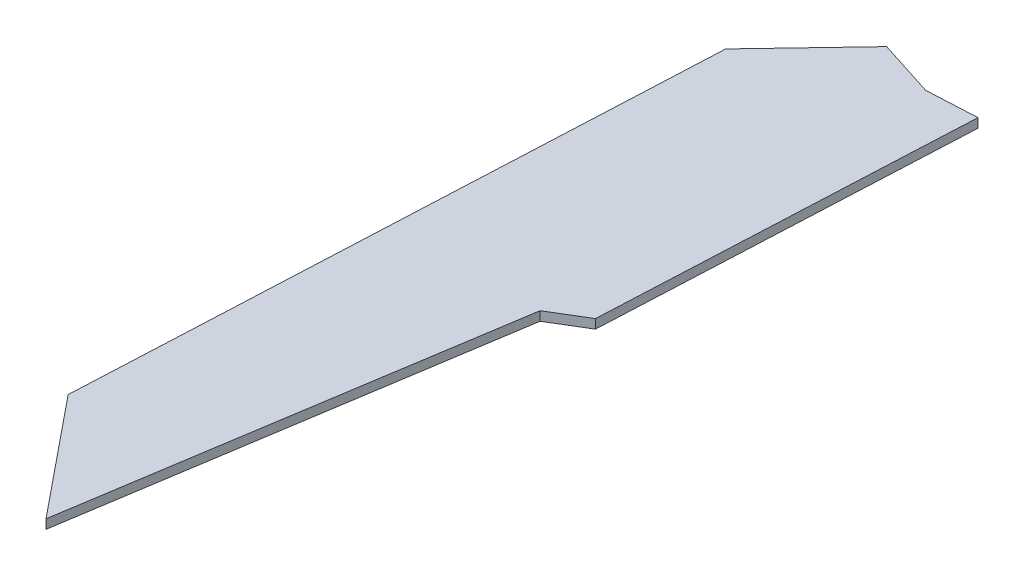
SolidWorks part; units mm, degrees
ref_plane "Plan de face" through (0, 0, 0) normal (0, 0, 1) x (1, 0, 0)
ref_plane "Plan de dessus" through (0, 0, 0) normal (0, 1, 0) x (1, 0, 0)
ref_plane "Plan de droite" through (0, 0, 0) normal (1, 0, 0) x (0, 0, -1)
sketch "Esquisse1" plane through (0, 0, 0) normal (0, 1, 0) x (1, 0, 0)
  line L0 (46.9058, 151.5265) -> (36.038, 150.9785)
  line L1 (36.038, 150.9785) -> (23.5382, 154.9847)
  line L2 (23.5382, 154.9847) -> (6.4202, 136.985)
  line L3 (6.4202, 136.985) -> (0, 0)
  line L4 (0, 0) -> (21.043, -25.8694)
  line L7 (21.043, -25.8694) -> (35.6157, 67.312)
  line L8 (35.6157, 67.312) -> (43.1464, 71.8656)
  line L9 (43.1464, 71.8656) -> (46.9058, 151.5265)
  point P5 (0, 0)
  point P6 (4.383, -5.2455)
  point P10 (0, 0)
  point P12 (20.006, -23.943)
  point P13 (20.7368, -25.8694)
extrude "Boss.-Extru.1" add sketch "Esquisse1" along normal blind 2
